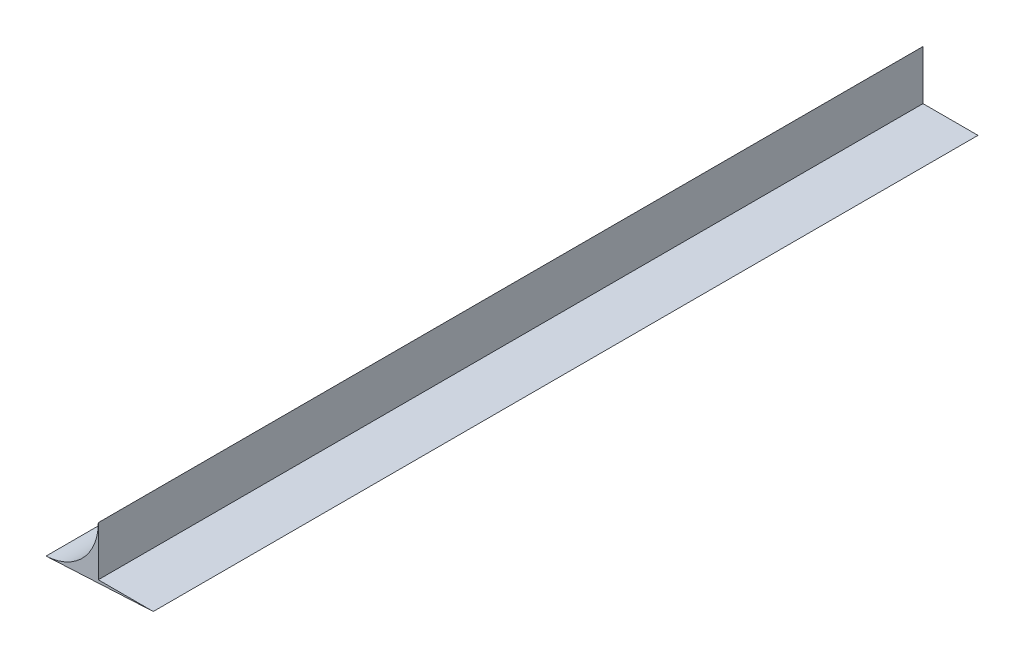
SolidWorks part; units mm, degrees
ref_plane "Front Plane" through (0, 0, 0) normal (0, 0, 1) x (1, 0, 0)
ref_plane "Top Plane" through (0, 0, 0) normal (0, 1, 0) x (1, 0, 0)
ref_plane "Right Plane" through (0, 0, 0) normal (1, 0, 0) x (0, 0, -1)
sketch "Sketch1" plane through (0, 0, 0) normal (0, 0, 1) x (1, 0, 0)
  line L1 (0, 0) -> (0, 13.5)
  line L2 (0, 0) -> (15, 0)
  line L3 (15, 0) -> (-14.2665, -1.5338)
  arc A0 (-14.2665, -1.5338) -> (0, 13.5) centre (-15.0544, 13.5) ccw
  point P5 (-9.1538, 0.582)
  point P7 (-9.3201, 0.5317)
  point P8 (0, 0)
  point P9 (0, 13)
  point P10 (-10.0228, -1.6343)
  dimension "D1" = 13.5
  dimension "D2" = 3
  dimension "D3" = 15
extrude "Boss-Extrude1" add sketch "Sketch1" along normal blind 225
